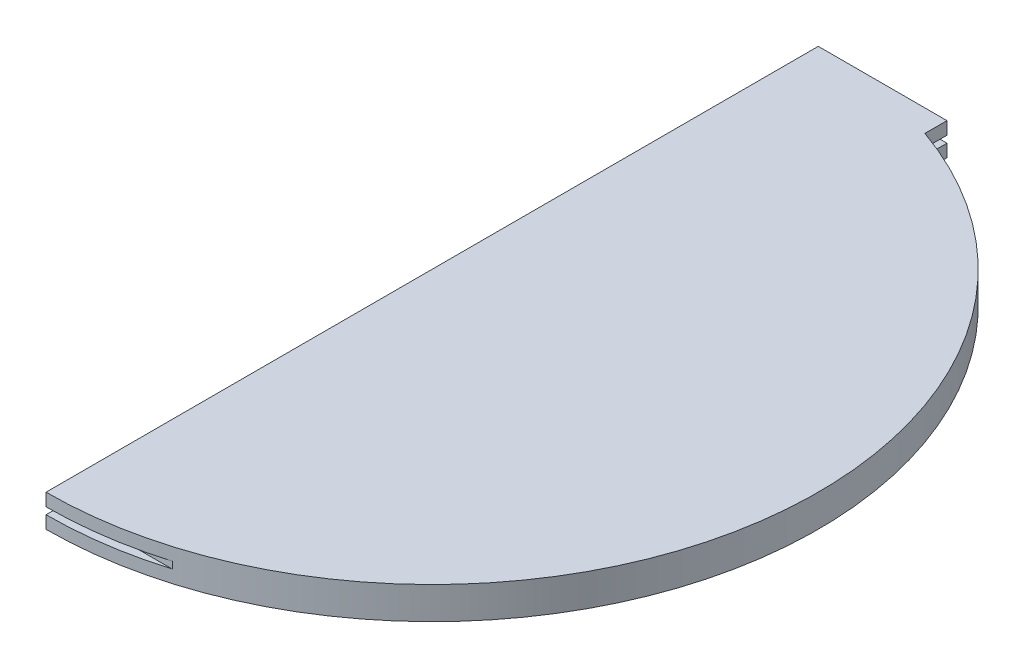
SolidWorks part; units mm, degrees
ref_plane "Front Plane" through (0, 0, 0) normal (0, 0, 1) x (1, 0, 0)
ref_plane "Top Plane" through (0, 0, 0) normal (0, 1, 0) x (1, 0, 0)
ref_plane "Right Plane" through (0, 0, 0) normal (1, 0, 0) x (0, 0, -1)
sketch "Sketch1" plane through (0, 0, 0) normal (0, 1, 0) x (1, 0, 0)
  line L0 (-228.6, 457.2) -> (-76.2, 457.2)
  line L2 (-228.6, -457.2) -> (-228.6, 457.2)
  line L5 (-228.6, -457.2) -> (228.6, 457.2) construction
  line L6 (-228.6, 457.2) -> (228.6, -457.2) construction
  line L7 (-76.2, 457.2) -> (-76.2, 431.0523)
  arc A0 (-76.2, 431.0523) -> (-228.6, -457.2) centre (-228.6, 0) cw
  point P0 (0, 0)
  dimension "D1" = 914.4
  dimension "D2" = 457.2
  dimension "D3" = 152.4
extrude "Boss-Extrude1" add sketch "Sketch1" along normal blind 38.1
sketch "Sketch2" plane through (-228.6, 0, 0) normal (-1, 0, 0) x (0, 0, 1)
  line L0 (457.2, 38.1) -> (457.2, 0) construction
  line L1 (438.15, 23.114) -> (476.25, 23.114)
  line L2 (438.15, 23.114) -> (438.15, 14.986)
  line L3 (438.15, 14.986) -> (476.25, 14.986)
  line L4 (476.25, 23.114) -> (476.25, 14.986)
  line L5 (438.15, 23.114) -> (476.25, 14.986) construction
  line L6 (438.15, 14.986) -> (476.25, 23.114) construction
  line L7 (0, -55) -> (0, 55) construction
  line L8 (-438.15, 14.986) -> (-476.25, 14.986)
  line L9 (-476.25, 23.114) -> (-476.25, 14.986)
  line L10 (-438.15, 23.114) -> (-476.25, 23.114)
  line L11 (-438.15, 23.114) -> (-438.15, 14.986)
  point P0 (457.2, 19.05)
  dimension "D1" = 8.128
  dimension "D2" = 38.1
extrude "Cut-Extrude1" cut sketch "Sketch2" against normal through all
